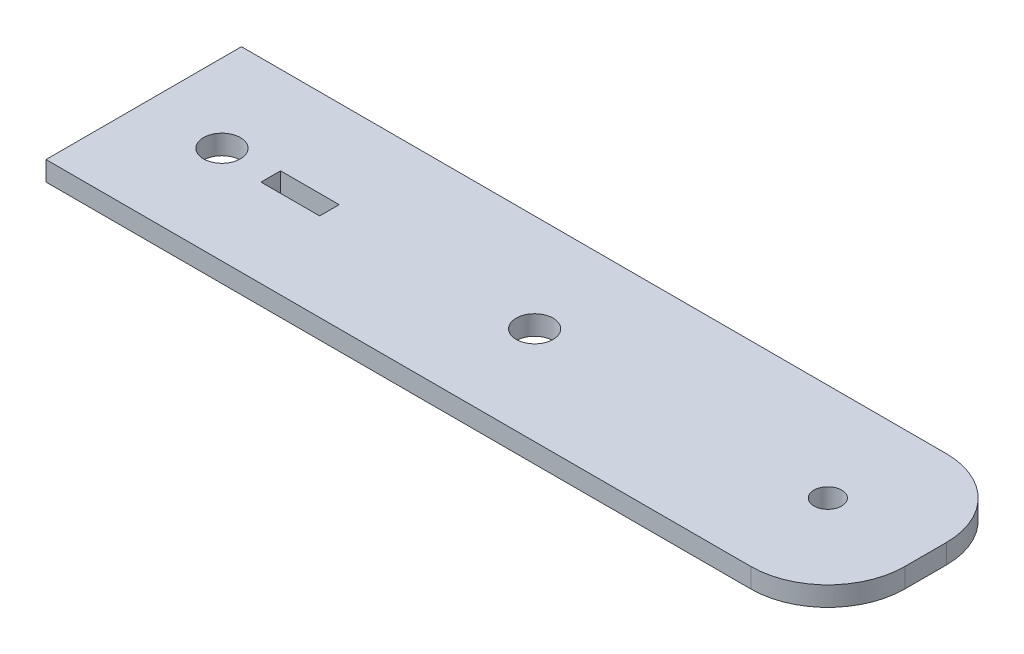
SolidWorks part; units mm, degrees
ref_plane "Front Plane" through (0, 0, 0) normal (0, 0, 1) x (1, 0, 0)
ref_plane "Top Plane" through (0, 0, 0) normal (0, 1, 0) x (1, 0, 0)
ref_plane "Right Plane" through (0, 0, 0) normal (1, 0, 0) x (0, 0, -1)
sketch "Sketch1" plane through (0, 0, 0) normal (0, 1, 0) x (1, 0, 0)
  line L1 (-12.7, -15.875) -> (101.8, -15.875)
  line L2 (-12.7, -15.875) -> (-12.7, 15.875)
  line L3 (-12.7, 15.875) -> (101.8, 15.875)
  line L4 (114.3, -3.375) -> (114.3, 3.375)
  line L5 (-12.7, -15.875) -> (114.3, 15.875) construction
  line L6 (-12.7, 15.875) -> (114.3, -15.875) construction
  line L7 (7.9375, -1.5875) -> (17.4625, -1.5875)
  line L8 (7.9375, -1.5875) -> (7.9375, 1.5875)
  line L9 (7.9375, 1.5875) -> (17.4625, 1.5875)
  line L10 (17.4625, -1.5875) -> (17.4625, 1.5875)
  line L11 (7.9375, -1.5875) -> (17.4625, 1.5875) construction
  line L12 (7.9375, 1.5875) -> (17.4625, -1.5875) construction
  circle A0 centre (0, 0) radius 3
  circle A1 centre (98.425, 0) radius 2.25
  arc A2 (101.8, -15.875) -> (114.3, -3.375) centre (101.8, -3.375) ccw
  arc A3 (101.8, 15.875) -> (114.3, 3.375) centre (101.8, 3.375) cw
  circle A4 centre (50.8, 0) radius 3
  point P0 (50.8, 0)
  point P19 (12.7, 0)
  dimension "D4" = 6
  dimension "D5" = 4.5
  dimension "D7" = 12.5
  dimension "D1" = 114.3
  dimension "D2" = 12.7
  dimension "D3" = 31.75
  dimension "D6" = 15.875
  dimension "D8" = 50.8
  dimension "D9" = 3.175
  dimension "D10" = 9.525
  dimension "D11" = 12.7
extrude "Boss-Extrude1" add sketch "Sketch1" along normal blind 3.175
